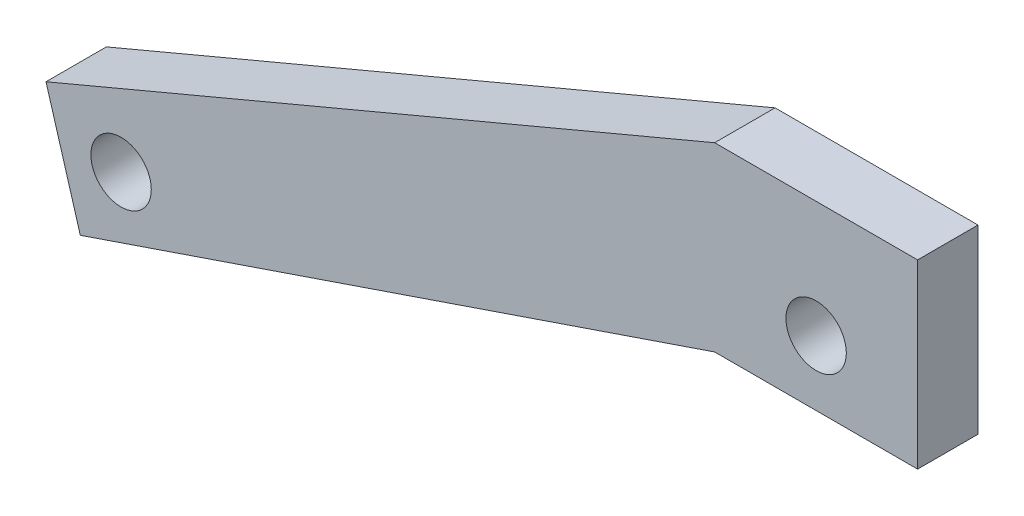
SolidWorks part; units mm, degrees
ref_plane "Front Plane" through (0, 0, 0) normal (0, 0, 1) x (1, 0, 0)
ref_plane "Top Plane" through (0, 0, 0) normal (0, 1, 0) x (1, 0, 0)
ref_plane "Right Plane" through (0, 0, 0) normal (1, 0, 0) x (0, 0, -1)
sketch "Sketch1" plane through (0, 0, 0) normal (0, 0, 1) x (1, 0, 0)
  line L0 (-111.2303, 107.8693) -> (-216.6614, 63.4815)
  line L2 (-265.4987, -57.803) -> (-268.7367, -55.0126) construction
  line L3 (-95.2303, 89.5169) -> (-204.8234, 57.0539) construction
  line L8 (-111.2303, 107.8693) -> (-111.2303, 79.2943) construction
  line L9 (-111.2303, 77.8693) -> (-79.2303, 77.8693) construction
  line L10 (-79.2303, 79.2943) -> (-79.2303, 107.8693)
  line L11 (-79.2303, 107.8693) -> (-111.2303, 107.8693)
  line L12 (-79.2303, 79.2943) -> (-111.2303, 79.2943)
  line L13 (-111.2303, 79.2943) -> (-211.2509, 45.2159)
  line L14 (-211.2509, 45.2159) -> (-216.6614, 63.4815)
  line L15 (-268.7367, -55.0126) -> (-242.2031, -37.4927) construction
  line L17 (-4.7666, 98.8499) -> (-114.0818, 113.4574) construction
  line L19 (-242.2031, -37.4927) -> (-208.8903, -37.4927) construction
  line L20 (-208.8903, -37.4927) -> (-111.2303, 107.8693) construction
  line L21 (-292.5067, -43.5335) -> (-248.9466, -55.1606) construction
  line L22 (-248.9466, -55.1606) -> (-208.8903, -56.2396) construction
  line L23 (-208.8903, -56.2396) -> (-14.9476, 79.2943) construction
  line L24 (-310.1435, -109.6088) -> (-95.2303, 89.5169) construction
  line L47 (-204.8234, 57.0539) -> (-213.9561, 54.3487) construction
  circle A1 centre (0, 39) radius 3.9687
  circle A2 centre (-95.2303, 89.5169) radius 4.7625
  circle A3 centre (-204.8234, 57.0539) radius 4.7625
  circle A4 centre (-310.1435, -109.6088) radius 68.3886 construction
  point P21 (-213.9561, 54.3487)
  dimension "D2" = 9.525
  dimension "D4" = 114.3
  dimension "D7" = 292.9825
  dimension "D3" = 9.525
  dimension "D5" = 19.05
  dimension "D6" = 28.575
  dimension "D8" = 106.5
  dimension "D9" = 32
extrude "Boss-Extrude1" add sketch "Sketch1" along normal blind 9.525
